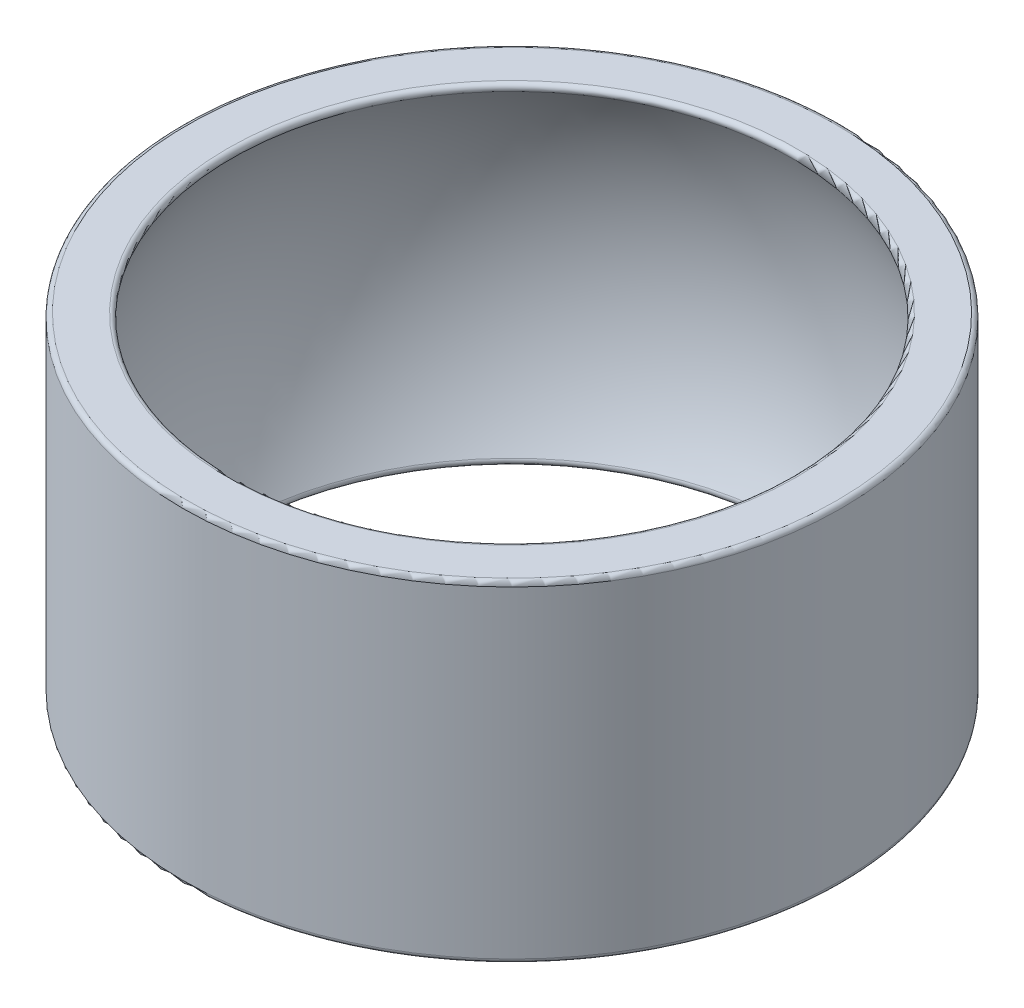
SolidWorks part; units mm, degrees
material "Copper"
ref_plane "Front Plane" through (0, 0, 0) normal (0, 0, 1) x (1, 0, 0)
ref_plane "Top Plane" through (0, 0, 0) normal (0, 1, 0) x (1, 0, 0)
ref_plane "Right Plane" through (0, 0, 0) normal (1, 0, 0) x (0, 0, -1)
sketch "Sketch1" plane through (0, 0, 0) normal (0, 0, 1) x (1, 0, 0)
  line L0 (0, 11) -> (0, -11) construction
  line L1 (0, 11) -> (18.3856, 11) construction
  line L2 (0, -11) -> (18.3856, -11) construction
  line L3 (18.3856, 11) -> (21.8918, 11)
  line L4 (18.3856, -11) -> (21.8918, -11)
  line L5 (21.8918, 11) -> (0, 0) construction
  line L6 (21.8918, 11) -> (21.8918, -11)
  arc A0 (18.3856, -11) -> (18.3856, 11) centre (0, 0) ccw
  point P3 (0, 0)
  dimension "D1" = 22
  dimension "D3" = 24.5
  dimension "D2" = 42.85
revolve "Revolve1" add sketch "Sketch1" angle 360 about L0
fillet "Fillet1" radius 0.3 4 edges at (-18.3856, 11, 0) (-18.3856, -11, 0) (-21.8918, -11, 0) (-21.8918, 11, 0)
equation "\"d\"= \"d3\" + \"Add\""
equation "\"Pitch\"= 2"
equation "\"C1\"= 22"
equation "\"d2\"= 55"
equation "\"dk\"= 42.85"
equation "\"Add\"= 1"
equation "\"d3\"= 24"
equation "\"D1@Sketch1\"=\"C1\""
equation "\"D3@Sketch1\"=(\"d2\" - 3 * \"Pitch\") / 2"
equation "\"D2@Sketch1\"=\"dk\""
